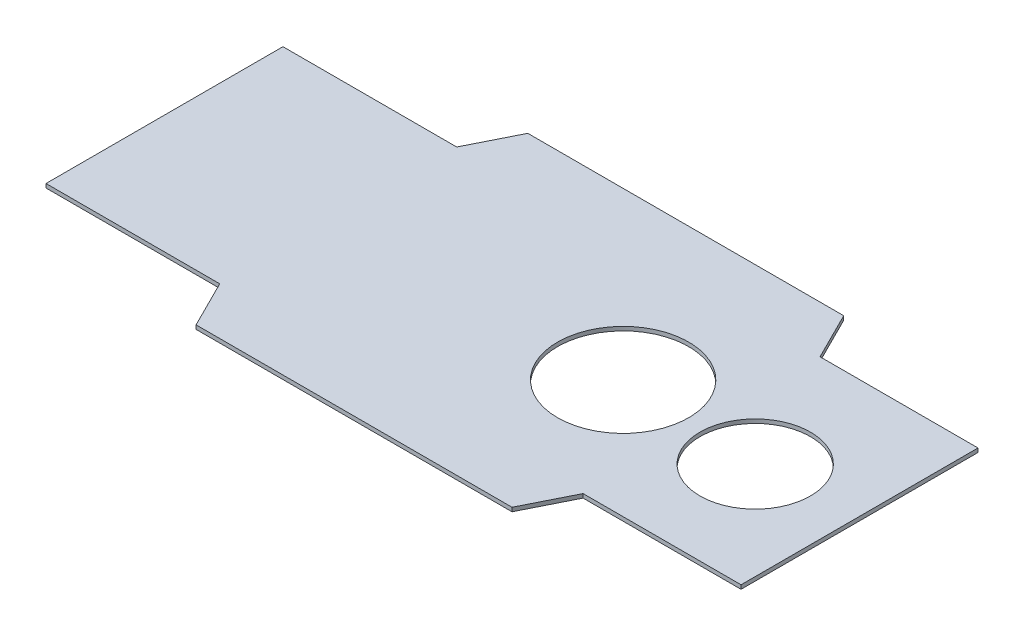
SolidWorks part; units mm, degrees
ref_plane "Front Plane" through (0, 0, 0) normal (0, 0, 1) x (1, 0, 0)
ref_plane "Top Plane" through (0, 0, 0) normal (0, 1, 0) x (1, 0, 0)
ref_plane "Right Plane" through (0, 0, 0) normal (1, 0, 0) x (0, 0, -1)
sketch "Sketch3" plane through (0, 0, 0) normal (0, 1, 0) x (1, 0, 0)
  line L0 (-279.4, 95.25) -> (-139.7, 95.25)
  line L1 (-279.4, -133.35) -> (279.4, -133.35) construction
  line L2 (-279.4, -133.35) -> (-279.4, 133.35) construction
  line L3 (-279.4, 133.35) -> (279.4, 133.35) construction
  line L4 (279.4, -133.35) -> (279.4, 133.35) construction
  line L5 (-279.4, -133.35) -> (279.4, 133.35) construction
  line L6 (-279.4, 133.35) -> (279.4, -133.35) construction
  line L7 (-279.4, -95.25) -> (279.4, -95.25) construction
  line L8 (-279.4, -95.25) -> (-279.4, 95.25) construction
  line L9 (-279.4, 95.25) -> (279.4, 95.25) construction
  line L10 (279.4, -95.25) -> (279.4, 95.25) construction
  line L13 (-139.7, 95.25) -> (-120.65, 133.35)
  line L14 (-120.65, 133.35) -> (133.35, 133.35)
  line L15 (133.35, 133.35) -> (152.4, 95.25)
  line L16 (152.4, 95.25) -> (279.4, 95.25)
  line L17 (-279.4, 95.25) -> (-279.4, -95.25)
  line L18 (279.4, 95.25) -> (279.4, -95.25)
  line L19 (-279.4, 0) -> (279.4, 0) construction
  line L20 (152.4, -95.25) -> (279.4, -95.25)
  line L21 (133.35, -133.35) -> (152.4, -95.25)
  line L22 (-120.65, -133.35) -> (133.35, -133.35)
  line L23 (-139.7, -95.25) -> (-120.65, -133.35)
  line L24 (-279.4, -95.25) -> (-139.7, -95.25)
  point P0 (0, 0)
  point P6 (0, 0)
  dimension "D1" = 266.7
  dimension "D2" = 558.8
  dimension "D3" = 190.5
  dimension "D4" = 127
  dimension "D5" = 139.7
  dimension "D6" = 254
extrude "Boss-Extrude1" add sketch "Sketch3" along normal mid plane 3.175
sketch "Sketch5" plane through (0, -1.5875, 0) normal (0, -1, 0) x (1, 0, 0)
  line L0 (-202.3532, 0) -> (279.4, 0) construction
  line L1 (-63.5, 25.4) -> (76.2, 25.4)
  line L2 (-63.5, 25.4) -> (-63.5, 88.9)
  line L3 (-63.5, 88.9) -> (76.2, 88.9)
  line L4 (76.2, 25.4) -> (76.2, 88.9)
  line L5 (-63.5, 25.4) -> (76.2, 88.9) construction
  line L6 (-63.5, 88.9) -> (76.2, 25.4) construction
  line L7 (279.4, 95.25) -> (279.4, -95.25) construction
  line L8 (-120.65, 133.35) -> (133.35, 133.35) construction
  line L9 (-120.65, 133.35) -> (133.35, 133.35) construction
  line L10 (6.35, 133.35) -> (6.35, 88.9) construction
  line L11 (-63.5, -88.9) -> (76.2, -88.9)
  line L12 (76.2, -25.4) -> (76.2, -88.9)
  line L13 (-63.5, -25.4) -> (76.2, -25.4)
  line L14 (-63.5, -25.4) -> (-63.5, -88.9)
  point P4 (6.35, 57.15)
  dimension "D1" = 63.5
  dimension "D2" = 139.7
  dimension "D3" = 44.45
sketch "Sketch6" plane through (0, 1.5875, 0) normal (0, 1, 0) x (1, 0, 0)
  line L0 (-279.4, 95.25) -> (-139.7, 95.25) construction
  line L1 (-120.65, 133.35) -> (-139.7, 95.25) construction
  line L2 (-139.7, 95.25) -> (-279.4, 95.25) construction
  line L3 (-139.7, 95.25) -> (-120.65, 133.35) construction
  line L4 (-120.65, 133.35) -> (133.35, 133.35) construction
  line L5 (133.35, 133.35) -> (152.4, 95.25) construction
  line L6 (152.4, 95.25) -> (279.4, 95.25) construction
  line L7 (279.4, 95.25) -> (279.4, -95.25) construction
  line L8 (279.4, -95.25) -> (152.4, -95.25) construction
  line L9 (133.35, -133.35) -> (152.4, -95.25) construction
  line L10 (152.4, -95.25) -> (279.4, -95.25) construction
  line L11 (152.4, -95.25) -> (133.35, -133.35) construction
  line L12 (133.35, -133.35) -> (-120.65, -133.35) construction
  line L13 (-120.65, -133.35) -> (-139.7, -95.25) construction
  line L14 (-139.7, -95.25) -> (-279.4, -95.25) construction
  line L15 (-279.4, -95.25) -> (-279.4, 95.25) construction
  line L16 (-276.225, 92.075) -> (-137.7377, 92.075)
  line L17 (-137.7377, 92.075) -> (-118.6877, 130.175)
  line L18 (-118.6877, 130.175) -> (131.3877, 130.175)
  line L19 (131.3877, 130.175) -> (150.4377, 92.075)
  line L20 (150.4377, 92.075) -> (276.225, 92.075)
  line L21 (276.225, 92.075) -> (276.225, -92.075)
  line L22 (276.225, -92.075) -> (150.4377, -92.075)
  line L23 (150.4377, -92.075) -> (131.3877, -130.175)
  line L24 (131.3877, -130.175) -> (-118.6877, -130.175)
  line L25 (-118.6877, -130.175) -> (-137.7377, -92.075)
  line L26 (-137.7377, -92.075) -> (-276.225, -92.075)
  line L27 (-276.225, -92.075) -> (-276.225, 92.075)
  dimension "D1" = 3.175
sketch "Sketch7" plane through (0, 1.5875, 0) normal (0, 1, 0) x (1, 0, 0)
  circle A1 centre (89.3496, 0) radius 52.705
  circle A3 centre (201.0298, -5.4936) radius 44.45
  dimension "D1" = 105.41
extrude "Cut-Extrude1" cut sketch "Sketch7" against normal blind 20.32
